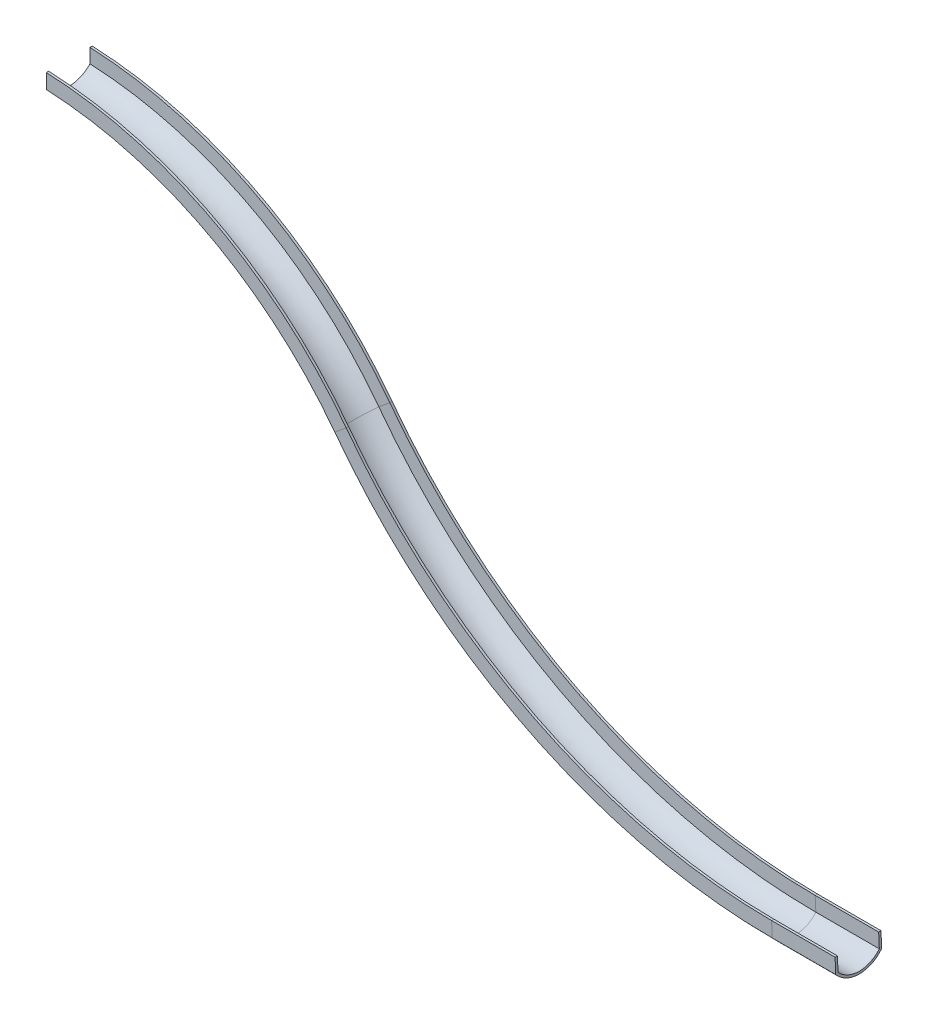
SolidWorks part; units mm, degrees
material "1060 Alloy"
ref_plane "Front" through (0, 0, 0) normal (0, 0, 1) x (1, 0, 0)
ref_plane "Top" through (0, 0, 0) normal (0, 1, 0) x (1, 0, 0)
ref_plane "Right" through (0, 0, 0) normal (1, 0, 0) x (0, 0, -1)
sketch "Sketch4" plane through (0, 0, 0) normal (1, 0, 0) x (0, 0, -1)
  line L0 (-442.4015, 250.0002) -> (-442.4015, 550.0002)
  line L1 (445.7839, 243.0936) -> (445.7839, 550.0002)
  line L2 (495.7839, 223.9977) -> (495.7839, 550.0002)
  line L3 (-492.4015, 231.3384) -> (-492.4015, 550.0002)
  line L4 (-492.4015, 550.0002) -> (-442.4015, 550.0002)
  line L5 (445.7839, 550.0002) -> (495.7839, 550.0002)
  arc A0 (-442.4015, 250.0002) -> (445.7839, 243.0936) centre (4.8284, 649.9821) ccw
  arc A1 (-492.4015, 231.3384) -> (495.7839, 223.9977) centre (4.8284, 649.9821) ccw
  point P3 (0.1629, 50.0002)
  point P11 (0, 0)
  dimension "D1" = 1000
  dimension "D2" = 600
  dimension "D3" = 300
  dimension "D4" = 200
  dimension "D5" = 50
sketch "Sketch6" plane through (0, 0, 0) normal (0, 0, 1) x (1, 0, 0)
  line L1 (15633.9403, -8000) -> (17000, -8000)
  arc A0 (0, 0) -> (6030.0365, -3194.792) centre (-372.5661, -7991.3199) cw
  arc A1 (6030.0365, -3194.792) -> (15633.9403, -8000) centre (15633.9403, 4000) ccw
  point P6 (0, 0)
  dimension "D2" = 8000
  dimension "D3" = 12000
  dimension "D1" = 7050
  dimension "D4" = 17000
  dimension "D5" = 8000
sweep "Sweep2" add profiles "Sketch4" path "Sketch6"
